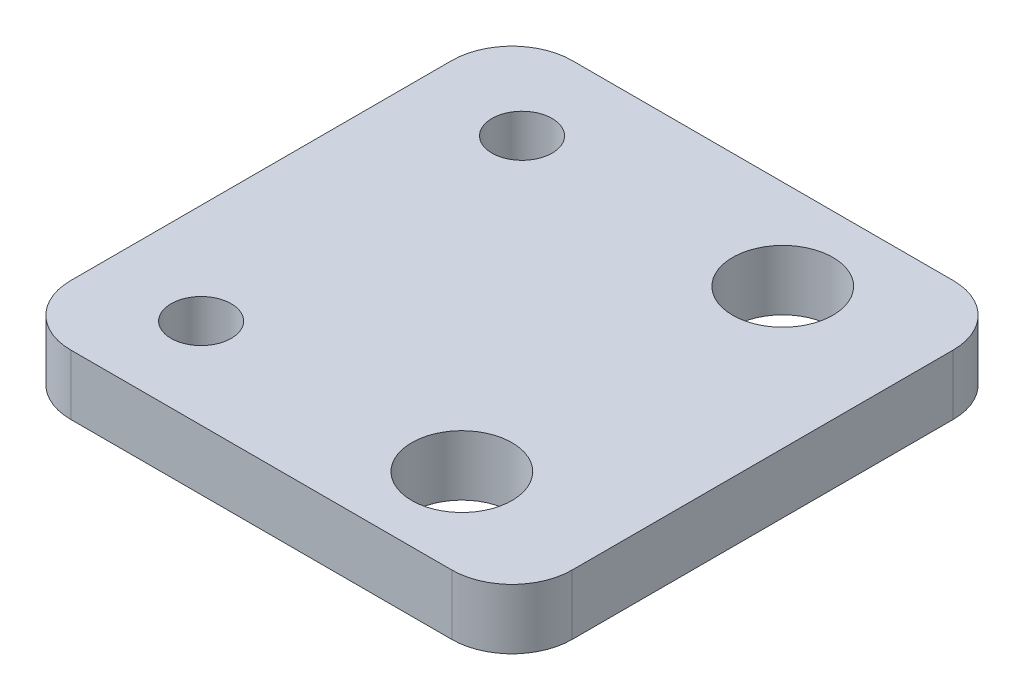
SolidWorks part; units mm, degrees
ref_plane "Front Plane" through (0, 0, 0) normal (0, 0, 1) x (1, 0, 0)
ref_plane "Top Plane" through (0, 0, 0) normal (0, 1, 0) x (1, 0, 0)
ref_plane "Right Plane" through (0, 0, 0) normal (1, 0, 0) x (0, 0, -1)
sketch "Sketch3" plane through (0, 0, 0) normal (0, 1, 0) x (1, 0, 0)
  line L0 (12.5, 0) -> (-12.5, 0) construction
  line L1 (-9.5, 12.5) -> (9.5, 12.5)
  line L2 (-12.5, 9.5) -> (-12.5, -9.5)
  line L3 (-9.5, -12.5) -> (9.5, -12.5)
  line L4 (12.5, 9.5) -> (12.5, -9.5)
  line L5 (-12.5, 12.5) -> (12.5, -12.5) construction
  line L6 (-12.5, -12.5) -> (12.5, 12.5) construction
  arc A0 (-9.5, 12.5) -> (-12.5, 9.5) centre (-9.5, 9.5) ccw
  arc A1 (-12.5, -9.5) -> (-9.5, -12.5) centre (-9.5, -9.5) ccw
  arc A2 (9.5, -12.5) -> (12.5, -9.5) centre (9.5, -9.5) ccw
  arc A3 (12.5, 9.5) -> (9.5, 12.5) centre (9.5, 9.5) ccw
  circle A4 centre (5.5, 8) radius 2.5
  circle A5 centre (5.5, -8) radius 2.5
  circle A6 centre (-7.5, 8) radius 1.5
  circle A7 centre (-7.5, -8) radius 1.5
  point P0 (0, 0)
  dimension "D1" = 3
  dimension "D3" = 25
  dimension "D4" = 7
  dimension "D5" = 8
  dimension "D6" = 8
  dimension "D7" = 13
  dimension "D8" = 13
  dimension "D2" = 25
extrude "Boss-Extrude1" add sketch "Sketch3" along normal blind 3
